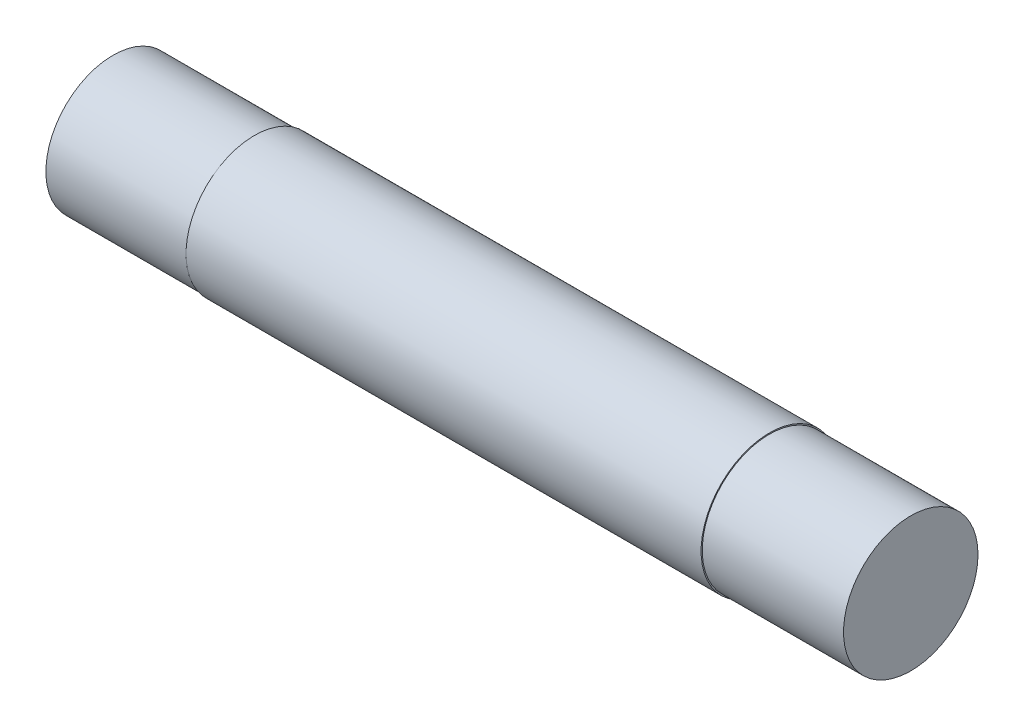
SolidWorks part; units mm, degrees
material "Brass"
ref_plane "Front Plane" through (0, 0, 0) normal (0, 0, 1) x (1, 0, 0)
ref_plane "Top Plane" through (0, 0, 0) normal (0, 1, 0) x (1, 0, 0)
ref_plane "Right Plane" through (0, 0, 0) normal (1, 0, 0) x (0, 0, -1)
sketch "Sketch1" plane through (0, 0, 0) normal (1, 0, 0) x (0, 0, -1)
  circle A0 centre (0, 0) radius 3.81
  dimension "D1" = 7.62
extrude "Boss-Extrude1" add sketch "Sketch1" along normal mid plane 44.45
sketch "Sketch2" plane through (22.225, 0, 0) normal (1, 0, 0) x (0, 0, -1)
  circle A0 centre (0, 0) radius 3.7465
  circle A1 centre (0, 0) radius 3.81 construction
  dimension "D1" = 7.493
extrude "Cut-Extrude-Thin3" cut sketch "Sketch2" against normal blind 7.874 thin
mirror "Mirror1" about plane through (0, 0, 0) normal (1, 0, 0) of "Cut-Extrude-Thin3"
